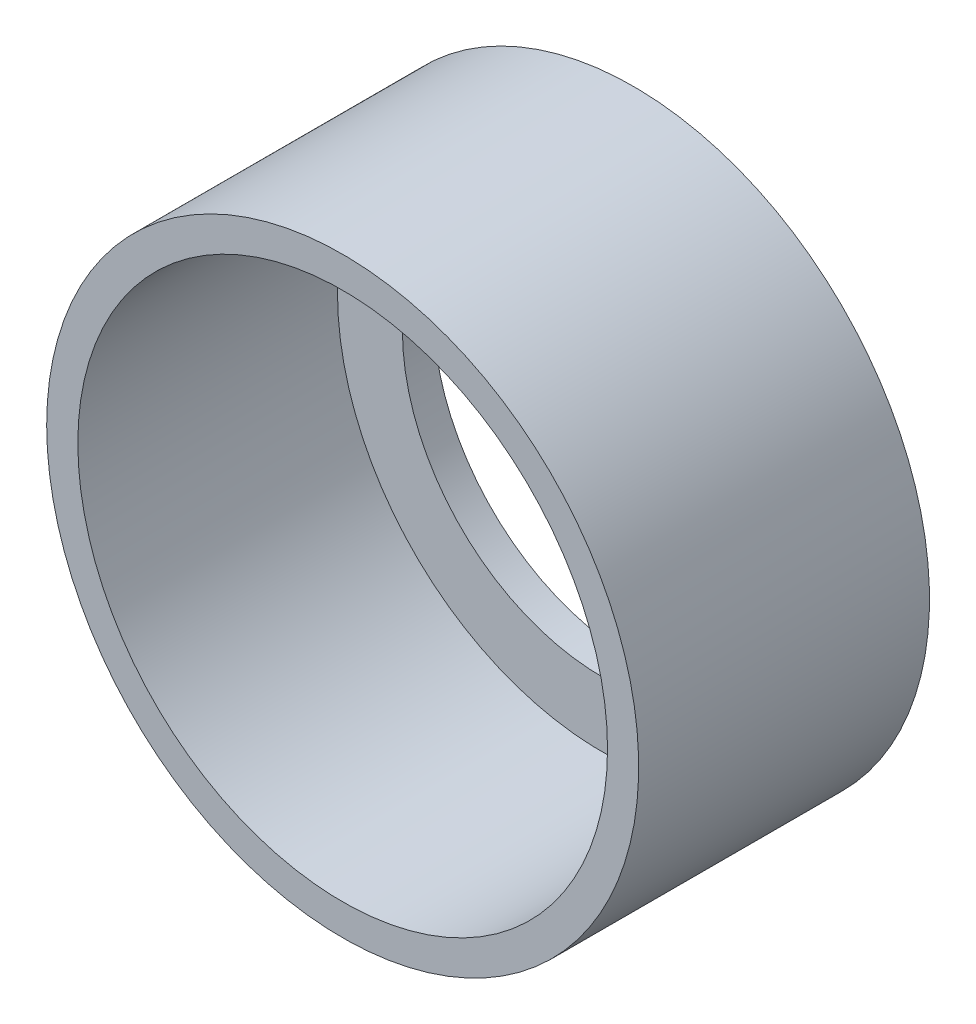
SolidWorks part; units mm, degrees
ref_plane "Front Plane" through (0, 0, 0) normal (0, 0, 1) x (1, 0, 0)
ref_plane "Top Plane" through (0, 0, 0) normal (0, 1, 0) x (1, 0, 0)
ref_plane "Right Plane" through (0, 0, 0) normal (1, 0, 0) x (0, 0, -1)
sketch "Sketch1" plane through (0, 0, 0) normal (0, 1, 0) x (1, 0, 0)
  line L0 (0, 10.179) -> (0, 0) construction
  line L1 (12.954, 5.4256) -> (14.478, 5.4256)
  line L2 (14.478, 5.4256) -> (14.478, 19.6496)
  line L3 (14.478, 19.6496) -> (9.779, 19.6496)
  line L4 (9.779, 19.6496) -> (9.779, 18.1256)
  line L5 (9.779, 18.1256) -> (12.954, 18.1256)
  line L6 (12.954, 18.1256) -> (12.954, 5.4256)
  dimension "D1" = 1.524
  dimension "D2" = 12.954
  dimension "D3" = 9.779
  dimension "D4" = 1.524
  dimension "D5" = 12.7
revolve "Revolve1" add sketch "Sketch1" angle 360 about L0
